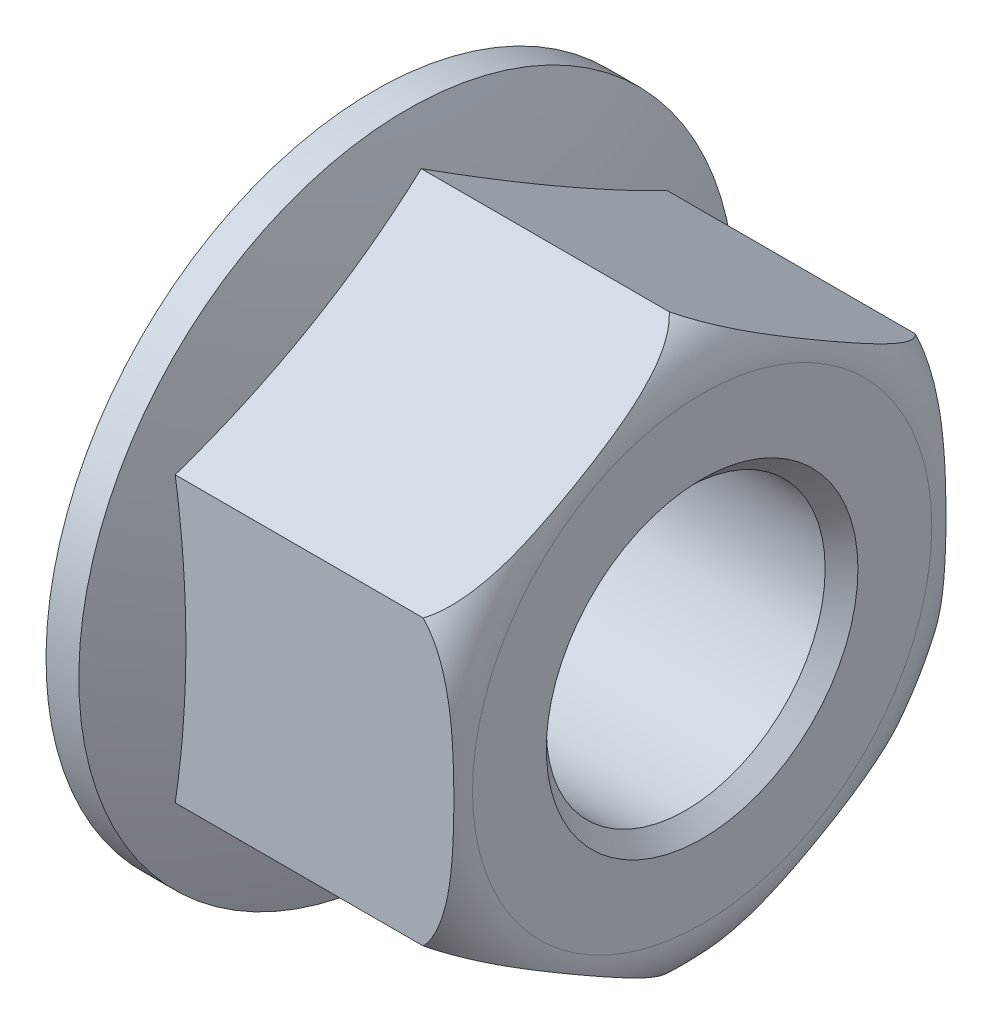
SolidWorks part; units mm, degrees
ref_plane "Plan de face" through (0, 0, 0) normal (0, 0, 1) x (1, 0, 0)
ref_plane "Plan de dessus" through (0, 0, 0) normal (0, 1, 0) x (1, 0, 0)
ref_plane "Plan de droite" through (0, 0, 0) normal (1, 0, 0) x (0, 0, -1)
sketch "Esquisse1" plane through (0, 0, 0) normal (1, 0, 0) x (0, 0, -1)
  line L1 (0, 8.6603) -> (-7.5, 4.3301)
  line L2 (-7.5, 4.3301) -> (-7.5, -4.3301)
  line L3 (-7.5, -4.3301) -> (0, -8.6603)
  line L4 (0, -8.6603) -> (7.5, -4.3301)
  line L5 (7.5, -4.3301) -> (7.5, 4.3301)
  line L6 (7.5, 4.3301) -> (0, 8.6603)
  circle A0 centre (0, 0) radius 7.5 construction
  dimension "D1" = 15
extrude "Extrusion1" add sketch "Esquisse1" along normal blind 10
sketch "Esquisse2" plane through (0, 0, 0) normal (0, 0, 1) x (1, 0, 0)
  line L0 (0, 0) -> (14.5886, 0) construction
  line L1 (10, 8.6603) -> (10, 4.3301) construction
  line L2 (10, 8.6603) -> (0, 8.6603) construction
  line L3 (10, 8.6603) -> (9, 8.6603)
  line L4 (10, 8.6603) -> (10, 7)
  arc A0 (10, 7) -> (9, 8.6603) centre (8.1218, 7) ccw
  dimension "D1" = 14
  dimension "D2" = 1
revolve "Enlèvement de matière-Révolution1" cut sketch "Esquisse2" angle 360 about L0
sketch "Esquisse3" plane through (0, 0, 0) normal (0, 0, 1) x (1, 0, 0)
  line L0 (0, 0) -> (0, 10)
  line L1 (0, 10) -> (1, 10)
  line L2 (0, 0) -> (2.7157, 0)
  line L3 (0, 0) -> (15.9891, 0) construction
  arc A0 (1, 10) -> (2.7157, 0) centre (-27.2843, 0) cw
  dimension "D3" = 30
  dimension "D1" = 1
  dimension "D2" = 20
revolve "Révolution1" add sketch "Esquisse3" angle 360 about L3
sketch "Esquisse4" plane through (0, 0, 0) normal (1, 0, 0) x (0, 0, -1)
  circle A0 centre (0, 0) radius 4.25
  dimension "D1" = 8.5
extrude "Enlèv. mat.-Extru.2" cut sketch "Esquisse4" along normal blind 10
chamfer "Chanfrein1" distance 0.5 angle 45 2 edges at (0, 0, -4.25) (10, 0, -4.25)
